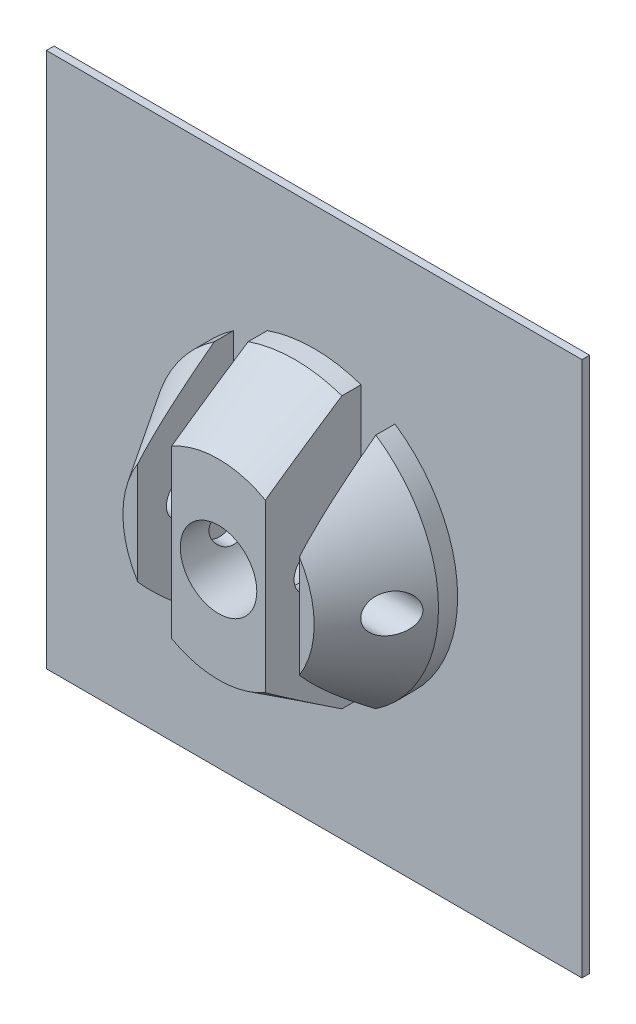
SolidWorks part; units mm, degrees
ref_plane "Alzado" through (0, 0, 0) normal (0, 0, 1) x (1, 0, 0)
ref_plane "Planta" through (0, 0, 0) normal (0, 1, 0) x (1, 0, 0)
ref_plane "Vista lateral" through (0, 0, 0) normal (1, 0, 0) x (0, 0, -1)
sketch "Croquis1" plane through (0, 0, 0) normal (0, 0, 1) x (1, 0, 0)
  line L1 (28, -28) -> (-28, -28)
  line L2 (28, -28) -> (28, 28)
  line L3 (28, 28) -> (-28, 28)
  line L4 (-28, -28) -> (-28, 28)
  line L5 (28, -28) -> (-28, 28) construction
  line L6 (28, 28) -> (-28, -28) construction
  circle A0 centre (0, 0) radius 2
  point P0 (0, 0)
  dimension "D3" = 4
  dimension "D1" = 56
  dimension "D2" = 56
extrude "Saliente-Extruir2" add sketch "Croquis1" along normal blind 0.8
ref_plane "Plano1" through (0, 0, 0) normal (1, 0, 0) x (0, 0, -1)
sketch "Croquis2" plane through (0, 0, 0) normal (1, 0, 0) x (0, 0, -1)
  line L0 (-0.8, 0) -> (-10.8, 0)
  line L1 (-0.8, 28) -> (-0.8, -28) construction
  line L2 (-10.8, 0) -> (-10.8, 10)
  line L3 (-0.8, 15) -> (-2.8, 15)
  line L4 (-0.8, 15) -> (-0.8, 0)
  line L5 (-2.8, 15) -> (-10.8, 10)
  dimension "D1" = 10
  dimension "D2" = 10
  dimension "D3" = 2
  dimension "D4" = 15
revolve "Revolución1" add sketch "Croquis2" angle 360 about L0
sketch "Croquis3" plane through (0, 0, 0.8) normal (0, 0, 1) x (1, 0, 0)
  line L2 (23, -28) -> (28, -28)
  line L3 (28, -28) -> (28, -23)
  arc A1 (23, -28) -> (28, -23) centre (28, -28) ccw
  dimension "D2" = 10
sketch "Croquis4" plane through (0, 0, 10.8) normal (0, 0, 1) x (1, 0, 0)
  line L0 (0, -0.44) -> (0, 0.44) construction
  line L1 (-8.45, 20) -> (-4.9, 20)
  line L2 (-8.45, 20) -> (-8.45, -20)
  line L3 (-8.45, -20) -> (-4.9, -20)
  line L4 (-4.9, 20) -> (-4.9, -20)
  line L5 (8.45, -20) -> (4.9, -20)
  line L6 (4.9, 20) -> (4.9, -20)
  line L7 (8.45, 20) -> (4.9, 20)
  line L8 (8.45, 20) -> (8.45, -20)
  circle A0 centre (0, 0) radius 4
  point P6 (-4.9, 0)
  dimension "D4" = 8
  dimension "D1" = 3.55
  dimension "D2" = 4.9
  dimension "D3" = 40
extrude "Cortar-Extruir1" cut sketch "Croquis4" against normal up to vertex (10 mm away) up to point (-28, 28, 0.8)
sketch "Croquis7" plane through (-28, 0, 0) normal (-1, 0, 0) x (0, 0, 1)
  line L0 (0.8, -12.3934) -> (0.8, 12.3934) construction
  circle A0 centre (5.8, 0) radius 2
  dimension "D1" = 4
  dimension "D2" = 5
extrude "Cortar-Extruir2" cut sketch "Croquis7" against normal up to vertex
extrude "Saliente-Extruir4" add sketch "Croquis3" against normal up to vertex
